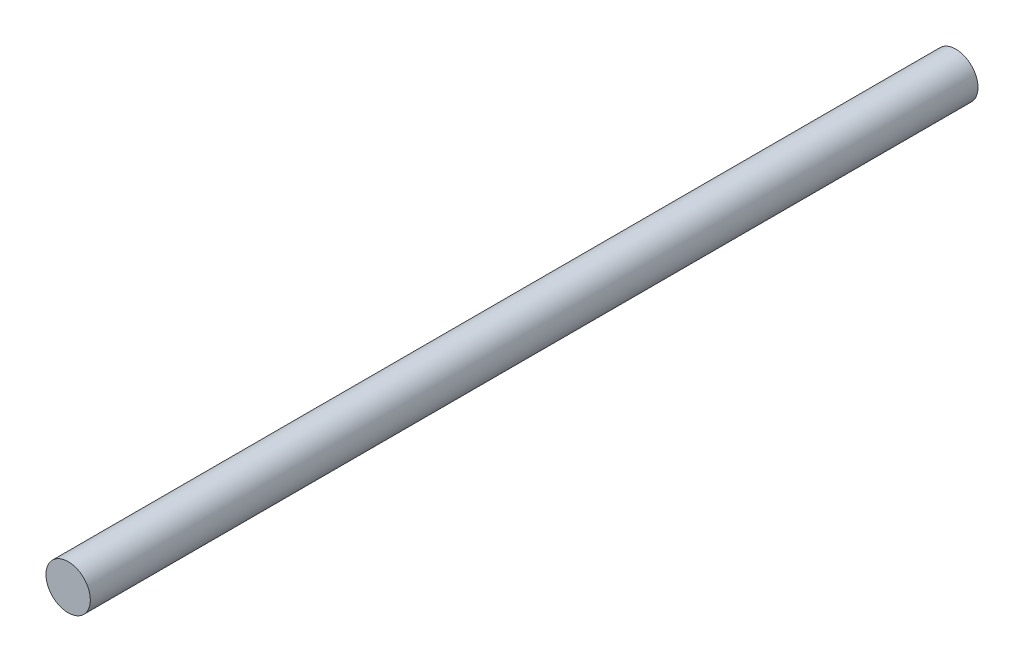
SolidWorks part; units mm, degrees
material "AISI 304"
ref_plane "Front Plane" through (0, 0, 0) normal (0, 0, 1) x (1, 0, 0)
ref_plane "Top Plane" through (0, 0, 0) normal (0, 1, 0) x (1, 0, 0)
ref_plane "Right Plane" through (0, 0, 0) normal (1, 0, 0) x (0, 0, -1)
sketch "Sketch1" plane through (0, 0, 0) normal (0, 0, 1) x (1, 0, 0)
  circle A0 centre (0, 0) radius 2
  dimension "D1" = 4
extrude "Boss-Extrude1" add sketch "Sketch1" along normal blind 80
